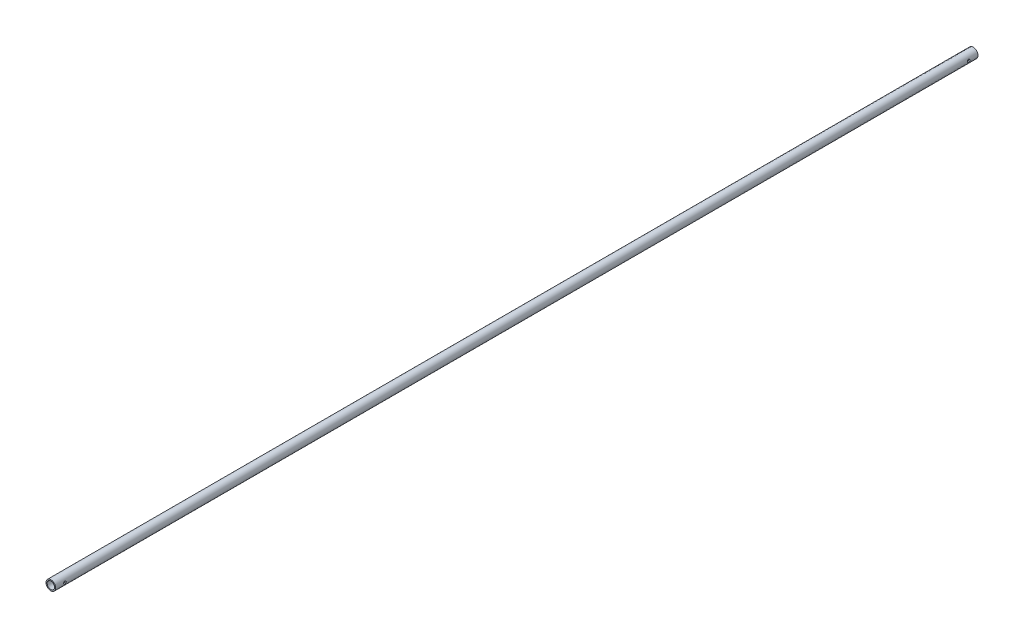
SolidWorks part; units mm, degrees
material "AISI 316 Barra de acero inoxidable recocido (SS)"
ref_plane "Alzado" through (0, 0, 0) normal (0, 0, 1) x (1, 0, 0)
ref_plane "Planta" through (0, 0, 0) normal (0, 1, 0) x (1, 0, 0)
ref_plane "Vista lateral" through (0, 0, 0) normal (1, 0, 0) x (0, 0, -1)
sketch "Croquis1" plane through (0, 0, 0) normal (0, 0, 1) x (1, 0, 0)
  circle A0 centre (0, 0) radius 12.5
  circle A1 centre (0, 0) radius 9.5
  dimension "D1" = 25
  dimension "D2" = 19
extrude "Saliente-Extruir1" add sketch "Croquis1" along normal blind 2380 and the other way blind 3 from offset 0
sketch "Croquis2" plane through (0, 0, 0) normal (1, 0, 0) x (0, 0, -1)
  line L0 (3, -12.5) -> (3, 12.5) construction
  line L1 (-2380, -12.5) -> (3, -12.5) construction
  circle A0 centre (-21, 0) radius 3.43
  dimension "D1" = 6.86
  dimension "D2" = 24
  dimension "D3" = 12.5
extrude "Cortar-Extruir1" cut sketch "Croquis2" against normal through all and the other way through all
sketch "Croquis3" plane through (0, 0, 0) normal (1, 0, 0) x (0, 0, -1)
  line L0 (3, 12.5) -> (-2380, 12.5) construction
  line L1 (-2380, 12.5) -> (-2380, -12.5) construction
  circle A0 centre (-2356, 0) radius 3.43
  dimension "D1" = 6.86
  dimension "D2" = 12.5
  dimension "D3" = 24
extrude "Cortar-Extruir2" cut sketch "Croquis3" against normal through all and the other way through all
